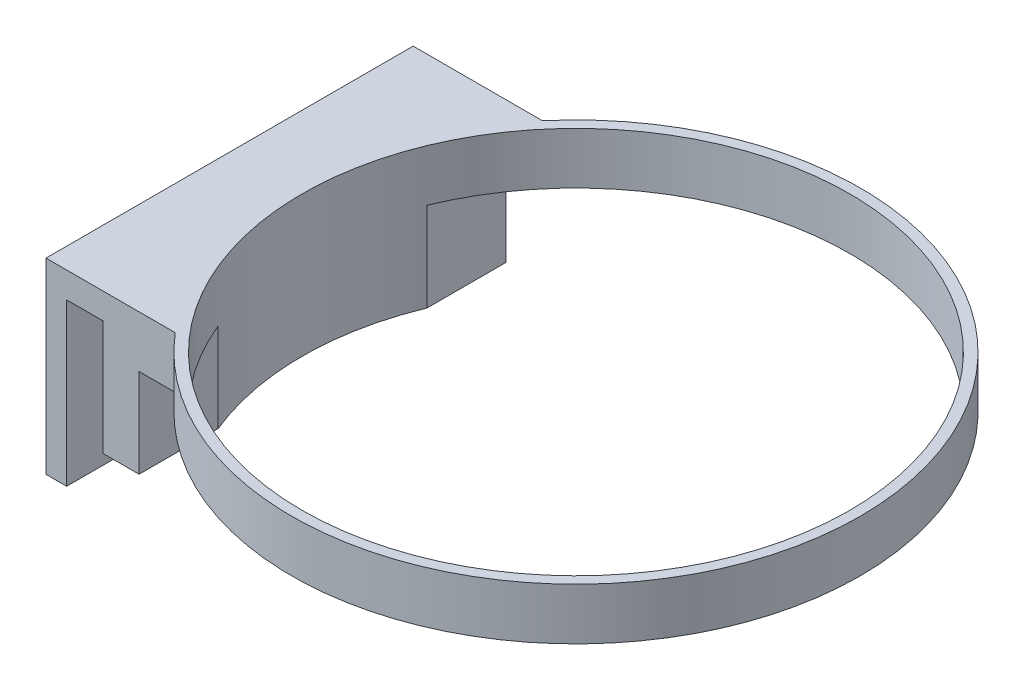
SolidWorks part; units mm, degrees
ref_plane "Front Plane" through (0, 0, 0) normal (0, 0, 1) x (1, 0, 0)
ref_plane "Top Plane" through (0, 0, 0) normal (0, 1, 0) x (1, 0, 0)
ref_plane "Right Plane" through (0, 0, 0) normal (1, 0, 0) x (0, 0, -1)
sketch "Sketch1" plane through (0, 0, 0) normal (0, 1, 0) x (1, 0, 0)
  line L1 (-42, 35.5106) -> (-56, 35.5106)
  line L3 (-42, -35.5106) -> (-56, -35.5106)
  line L4 (-56, 35.5106) -> (-56, -35.5106)
  line L5 (-49, -35.5106) -> (-49, 35.5106) construction
  line L6 (-41.8824, 0) -> (-56, 0) construction
  circle A0 centre (0, 0) radius 53
  arc A1 (-42, -35.5106) -> (-42, 35.5106) centre (0, 0) ccw
  point P3 (0, 0)
  point P8 (0, 0)
  point P9 (0, 0)
  point P10 (0, 0)
  point P11 (0, 0)
  point P608 (-49, 0)
  dimension "D1" = 110
  dimension "D2" = 106
  dimension "D3" = 14
  dimension "D4" = 56
extrude "Boss-Extrude1" add sketch "Sketch1" along normal blind 10
sketch "Sketch3" plane through (0, 0, -35.5106) normal (0, 0, -1) x (-1, 0, 0)
  line L0 (49, 0) -> (49, -17.2171)
  line L1 (42, 0) -> (56, 0) construction
  line L2 (49, -17.2171) -> (56, -17.2171)
  line L3 (56, -17.2171) -> (56, 5)
  line L4 (56, 10) -> (56, 0) construction
  line L5 (56, 5) -> (63, 5)
  line L6 (63, 5) -> (63, -26.229)
  line L7 (63, -26.229) -> (67, -26.229)
  line L8 (67, -26.229) -> (67, 10)
  line L9 (67, 10) -> (49, 10)
  line L10 (42, 10) -> (56, 10) construction
  line L11 (49, 10) -> (49, 0)
  dimension "D1" = 7
  dimension " 4" = 4
extrude "Boss-Extrude2" add sketch "Sketch3" against normal up to surface (71.0211 mm away) up to face at (-49, 5, 35.5106)
sketch "Sketch4" plane through (0, 10, 0) normal (0, 1, 0) x (1, 0, 0)
  circle A0 centre (0, 0) radius 53
extrude "Cut-Extrude1" cut sketch "Sketch4" against normal up to surface (27.2171 mm away) up to face at (-52.5, -17.2171, 0)
